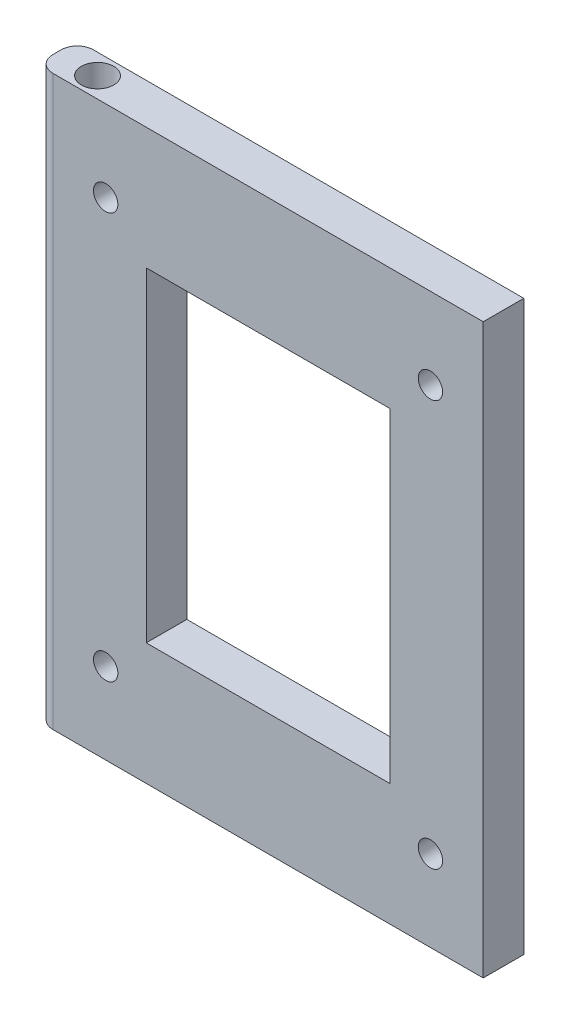
SolidWorks part; units mm, degrees
ref_plane "Front Plane" through (0, 0, 0) normal (1, 0, 0) x (0, 1, 0)
ref_plane "Top Plane" through (0, 0, 0) normal (0, 0, 1) x (0, 1, 0)
ref_plane "Right Plane" through (0, 0, 0) normal (0, 1, 0) x (-1, 0, 0)
sketch "Sketch1" plane through (0, 0, 0) normal (0, 0, 1) x (0, 1, 0)
  line L1 (0, 0) -> (70, 0)
  line L2 (0, 0) -> (0, 55)
  line L3 (0, 55) -> (70, 55)
  line L4 (70, 0) -> (70, 55)
  dimension "D1" = 55
  dimension "D2" = 70
extrude "Boss-Extrude1" add sketch "Sketch1" along normal blind 5
sketch "Sketch2" plane through (0, 70, 0) normal (0, 1, 0) x (-1, 0, 0)
  line L0 (55, 2.5) -> (50, 2.5) construction
  line L1 (55, 5) -> (55, 0) construction
  line L2 (50, 5) -> (50, 2.5) construction
  line L3 (0, 5) -> (55, 5) construction
  circle A0 centre (50, 2.5) radius 2
  dimension "D1" = 4
  dimension "D2" = 5
extrude "Cut-Extrude1" cut sketch "Sketch2" against normal blind 4.5
sketch "Sketch3" plane through (0, 0, 0) normal (0, -1, 0) x (1, 0, 0)
  line L0 (-55, 2.5) -> (-50, 2.5) construction
  line L1 (-55, 5) -> (-55, 0) construction
  line L2 (-50, 2.5) -> (-50, 5) construction
  line L3 (-55, 5) -> (0, 5) construction
  circle A0 centre (-50, 2.5) radius 2
  dimension "D1" = 4
  dimension "D2" = 5
extrude "Cut-Extrude2" cut sketch "Sketch3" against normal blind 4.5
fillet "Fillet1" radius 2 2 edges at (-55, 35, 0) (-55, 35, 5)
sketch "Sketch4" plane through (0, 0, 5) normal (0, 0, 1) x (1, 0, 0)
  line L0 (-6.5, 70) -> (-6.5, 0) construction
  line L1 (0, 70) -> (-53, 70) construction
  line L2 (-53, 0) -> (0, 0) construction
  line L3 (-6.5, 60) -> (-53, 60) construction
  line L5 (-53, 70) -> (-53, 0) construction
  line L6 (-26.5, 70) -> (-26.5, 0) construction
  line L7 (-6.5, 35) -> (-53, 35) construction
  line L9 (-41.5, 15) -> (-11.5, 15)
  line L10 (-41.5, 15) -> (-41.5, 55)
  line L11 (-41.5, 55) -> (-11.5, 55)
  line L12 (-11.5, 15) -> (-11.5, 55)
  line L13 (-41.5, 15) -> (-11.5, 55) construction
  line L14 (-41.5, 55) -> (-11.5, 15) construction
  circle A0 centre (-6.5, 60) radius 1.5
  circle A1 centre (-46.5, 60) radius 1.5
  circle A2 centre (-6.5, 10) radius 1.5
  circle A3 centre (-46.5, 10) radius 1.5
  point P21 (-26.5, 35)
  dimension "D3" = 3
  dimension "D1" = 20
  dimension "D2" = 25
  dimension "D4" = 30
  dimension "D5" = 40
extrude "Cut-Extrude3" cut sketch "Sketch4" against normal through all
